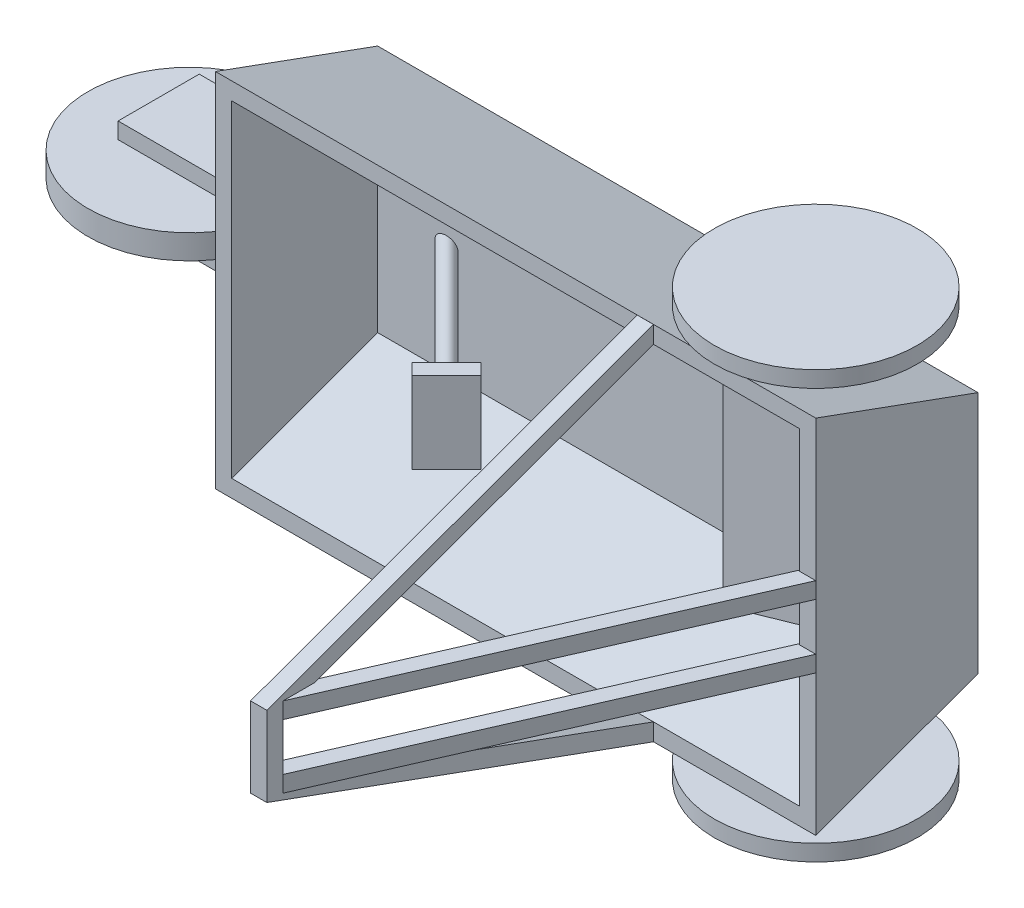
SolidWorks part; units mm, degrees
ref_plane "Front" through (0, 0, 0) normal (0, 0, 1) x (1, 0, 0)
ref_plane "Top" through (0, 0, 0) normal (0, 1, 0) x (1, 0, 0)
ref_plane "Right" through (0, 0, 0) normal (1, 0, 0) x (0, 0, -1)
sketch "Sketch1" plane through (0, 0, 0) normal (0, 0, 1) x (1, 0, 0)
  line L1 (0, 0) -> (-88.9, 0)
  line L2 (0, 0) -> (0, 38.1)
  line L3 (0, 38.1) -> (-88.9, 38.1)
  line L4 (-88.9, 0) -> (-88.9, 38.1)
  dimension "D1" = 88.9
  dimension "D2" = 38.1
extrude "Boss-Extrude1" add sketch "Sketch1" along normal blind 2.54
sketch "Sketch2" plane through (-88.9, 0, 0) normal (-1, 0, 0) x (0, 0, 1)
  line L0 (0, 0) -> (25.4, -9.2448)
  line L1 (25.4, -6.5418) -> (2.54, 1.7785)
  line L2 (2.54, 38.1) -> (2.54, 0) construction
  line L3 (25.4, -6.5418) -> (25.4, -9.2448)
  line L4 (2.54, 1.7785) -> (0, 0)
  line L5 (0, 38.1) -> (25.4, 47.3448)
  line L6 (25.4, 47.3448) -> (25.4, 44.6418)
  line L7 (25.4, 44.6418) -> (2.54, 36.3215)
  line L8 (2.54, 36.3215) -> (0, 38.1)
  line L9 (0, 38.1) -> (0, 0) construction
  dimension "D1" = 110
  dimension "D2" = 110
  dimension "D3" = 2.54
  dimension "D4" = 2.54
  dimension "D5" = 25.4
extrude "Boss-Extrude2" add sketch "Sketch2" against normal through all
sketch "Sketch3" plane through (0, 0, 0) normal (1, 0, 0) x (0, 0, -1)
  line L0 (-25.4, -9.2448) -> (0, 0)
  line L1 (0, 0) -> (0, 38.1)
  line L2 (0, 38.1) -> (-25.4, 47.3448)
  line L3 (-25.4, 47.3448) -> (-25.4, -9.2448)
extrude "Boss-Extrude3" add sketch "Sketch3" along normal blind 2.54
ref_plane "Plane1" through (0, 47.3448, 0) normal (0, 1, 0) x (-1, 0, 0)
sketch "Sketch5" plane through (0, 47.3448, 0) normal (0, 1, 0) x (-1, 0, 0)
  line L0 (-2.54, 0) -> (-2.54, 25.4) construction
  line L1 (-2.54, 0) -> (88.9, 0) construction
  circle A0 centre (10.16, 12.7) radius 2.54
  dimension "D2" = 5.08
  dimension "D1" = 12.7
  dimension "D3" = 12.7
extrude "Boss-Extrude4" add sketch "Sketch5" along normal blind 2.54 and the other way up to next
sketch "Sketch6" plane through (0, 49.8848, 0) normal (0, 1, 0) x (1, 0, 0)
  circle A0 centre (-10.16, -12.7) radius 15.875
  dimension "D1" = 31.75
extrude "Boss-Extrude5" add sketch "Sketch6" along normal blind 2.54
ref_plane "Plane2" through (0, 19.05, 0) normal (0, -1, 0) x (-1, 0, 0)
sketch "Sketch7" plane through (-88.9, 0, 0) normal (-1, 0, 0) x (0, 0, 1)
  line L0 (25.4, 47.3448) -> (25.4, 19.05)
  line L1 (25.4, 44.6418) -> (25.4, 47.3448) construction
  line L2 (25.4, 19.05) -> (0, 19.05)
  line L4 (25.4, 47.3448) -> (0, 38.1)
  line L5 (0, 38.1) -> (0, 19.05)
  line L6 (0, 38.1) -> (0, 0) construction
  line L9 (-41.91, 19.05) -> (41.91, 19.05) construction
extrude "Boss-Extrude6" add sketch "Sketch7" along normal blind 2.54
mirror "Mirror1" about plane through (0, 19.05, 0) normal (0, -1, 0) of "Boss-Extrude6", "Boss-Extrude5", "Boss-Extrude4"
sketch "Sketch8" plane through (-91.44, 0, 0) normal (-1, 0, 0) x (0, 0, 1)
  line L1 (17.78, 22.86) -> (5.08, 22.86)
  line L2 (17.78, 22.86) -> (17.78, 25.4)
  line L3 (17.78, 25.4) -> (5.08, 25.4)
  line L4 (5.08, 22.86) -> (5.08, 25.4)
  line L6 (5.08, 15.24) -> (17.78, 15.24)
  line L7 (5.08, 15.24) -> (5.08, 12.7)
  line L8 (5.08, 12.7) -> (17.78, 12.7)
  line L9 (17.78, 15.24) -> (17.78, 12.7)
  line L10 (0, 38.1) -> (0, 0) construction
  line L12 (12.7, 42.7224) -> (12.7, -4.6224) construction
  line L13 (25.4, 47.3448) -> (0, 38.1) construction
  line L14 (25.4, -9.2448) -> (0, 0) construction
  point P16 (12.7, 19.05)
  dimension "D4" = 2.54
  dimension "D1" = 12.7
  dimension "D2" = 12.7
  dimension "D3" = 5.08
  dimension "D5" = 2.54
  dimension "D6" = 3.81
  dimension "D7" = 3.81
extrude "Boss-Extrude7" add sketch "Sketch8" along normal blind 22.86
sketch "Sketch9" plane through (0, 12.7, 0) normal (0, -1, 0) x (-1, 0, 0)
  line L0 (114.3, -5.08) -> (114.3, -17.78) construction
  circle A0 centre (109.22, -11.6998) radius 2.54
  dimension "D1" = 5.08
  dimension "D2" = 5.08
extrude "Boss-Extrude8" add sketch "Sketch9" against normal up to surface (12.7 mm away) up to face at (-102.87, 25.4, 11.43)
sketch "Sketch11" plane through (0, 19.05, 0) normal (0, -1, 0) x (-1, 0, 0)
  circle A0 centre (109.22, -11.6998) radius 15.875
  circle A2 centre (109.22, -11.6998) radius 2.54 construction
  dimension "D1" = 31.75
extrude "Boss-Extrude9" add sketch "Sketch11" along normal blind 1.905 and the other way blind 1.905
ref_plane "Plane3" through (0, -2.9413, 8.0812) normal (0, 0.342, -0.9397) x (-1, 0, 0)
sketch "Sketch13" plane through (0, -2.9413, 8.0812) normal (0, 0.342, -0.9397) x (-1, 0, 0)
  line L0 (0, 50.6369) -> (88.9, 50.6369) construction
  line L1 (25.4, 50.6369) -> (22.86, 50.6369)
  line L2 (25.4, 50.6369) -> (25.4, 53.1705)
  line L3 (25.4, 53.1705) -> (22.86, 53.1705)
  line L4 (22.86, 50.6369) -> (22.86, 53.1705)
  line L5 (-2.54, 53.1769) -> (-2.54, 0) construction
  dimension "D1" = 2.5336
  dimension "D2" = 2.54
  dimension "D3" = 25.4
extrude "Boss-Extrude10" add sketch "Sketch13" against normal blind 63.5 and the other way up to next separate body
ref_plane "Plane4" through (0, 7.3982, 20.3263) normal (0, 0.342, 0.9397) x (-1, 0, 0)
sketch "Sketch16" plane through (0, 7.3982, 20.3263) normal (0, 0.342, 0.9397) x (-1, 0, 0)
  line L0 (0, 14.8346) -> (88.9, 14.8346) construction
  line L1 (25.4, 14.8346) -> (22.86, 14.8346)
  line L2 (25.4, 14.8346) -> (25.4, 17.3746)
  line L3 (25.4, 17.3746) -> (22.86, 17.3746)
  line L4 (22.86, 14.8346) -> (22.86, 17.3746)
  line L5 (-2.54, -35.8023) -> (-2.54, 17.3746) construction
  dimension "D1" = 27.94
  dimension "D2" = 2.54
  dimension "D3" = 2.54
extrude "Boss-Extrude12" add sketch "Sketch16" along normal blind 63.5 and the other way up to next
sketch "Sketch18" plane through (0, 19.05, 0) normal (0, -1, 0) x (-1, 0, 0)
  line L0 (25.4, -85.0705) -> (25.4, -85.9392) construction
  line L1 (25.4, -83.3992) -> (22.86, -83.3992)
  line L2 (25.4, -83.3992) -> (25.4, -85.9392)
  line L3 (25.4, -85.9392) -> (22.86, -85.9392)
  line L4 (22.86, -83.3992) -> (22.86, -85.9392)
  line L5 (25.4, -85.9392) -> (22.86, -85.9392) construction
  line L6 (22.86, -85.9392) -> (22.86, -85.0705) construction
  dimension "D1" = 2.54
extrude "Boss-Extrude14" add sketch "Sketch18" along normal up to surface and the other way up to surface
ref_plane "Plane5" through (11.4648, 0, 5.0209) normal (-0.916, 0, -0.4012) x (-0.4012, 0, 0.916)
sketch "Sketch19" plane through (11.4648, 0, 5.0209) normal (-0.916, 0, -0.4012) x (-0.4012, 0, 0.916)
  line L0 (22.2477, 47.3448) -> (22.2477, -9.2448) construction
  line L1 (87.8916, 12.7896) -> (22.2477, 12.7896)
  line L2 (87.8916, 12.7896) -> (87.8916, 15.3296)
  line L3 (87.8916, 15.3296) -> (22.2477, 15.3296)
  line L4 (22.2477, 12.7896) -> (22.2477, 15.3296)
  line L6 (87.8916, 25.3036) -> (22.2477, 25.3036)
  line L7 (87.8916, 25.3036) -> (87.8916, 22.7636)
  line L8 (87.8916, 22.7636) -> (22.2477, 22.7636)
  line L9 (22.2477, 25.3036) -> (22.2477, 22.7636)
  dimension "D1" = 2.54
  dimension "D2" = 2.54
extrude "Boss-Extrude15" add sketch "Sketch19" along normal blind 2.54
sketch "Sketch20" plane through (-25.4, 0, 0) normal (-1, 0, 0) x (0, 0, 1)
  line L1 (85.9392, 25.3036) -> (80.2877, 25.3036)
  line L2 (85.9392, 25.3036) -> (85.9392, 11.7464)
  line L3 (85.9392, 11.7464) -> (80.2877, 11.7464)
  line L4 (80.2877, 25.3036) -> (80.2877, 11.7464)
extrude "Cut-Extrude1" cut sketch "Sketch20" along normal blind 2.54
ref_plane "Plane6" through (-43.18, 0, -43.18) normal (0.7071, 0, 0.7071) x (0, -1, 0)
sketch "Sketch21" plane through (-43.18, 0, -43.18) normal (0.7071, 0, 0.7071) x (0, -1, 0)
  line L1 (-19.05, -48.895) -> (-19.05, 48.895) construction
  line L3 (-36.3215, -64.6578) -> (-1.7785, -64.6578) construction
  circle A0 centre (-19.05, -57.0378) radius 1.27
  dimension "D2" = 2.54
  dimension "D1" = 7.62
extrude "Boss-Extrude16" add sketch "Sketch21" along normal blind 39.116
sketch "Sketch22" plane through (0, 0, 0) normal (0, 0, -1) x (-1, 0, 0)
  line L1 (84.8073, 12.4754) -> (75.0849, 12.4754)
  line L2 (84.8073, 12.4754) -> (84.8073, 29.6888)
  line L3 (84.8073, 29.6888) -> (75.0849, 29.6888)
  line L4 (75.0849, 12.4754) -> (75.0849, 29.6888)
extrude "Cut-Extrude2" cut sketch "Sketch22" along normal blind 39.116
sketch "Sketch23" plane through (-15.5208, 0, -15.5208) normal (0.7071, 0, 0.7071) x (0.7071, 0, -0.7071)
  line L1 (-60.8478, 25.4) -> (-53.2278, 25.4)
  line L2 (-60.8478, 25.4) -> (-60.8478, 12.7)
  line L3 (-60.8478, 12.7) -> (-53.2278, 12.7)
  line L4 (-53.2278, 25.4) -> (-53.2278, 12.7)
  point P4 (-57.0378, 19.05)
  point P7 (-57.0378, 25.4)
  point P9 (-60.8478, 19.05)
  dimension "D1" = 12.7
  dimension "D2" = 7.62
extrude "Boss-Extrude17" add sketch "Sketch23" along normal blind 2.54
ref_plane "Plane7" through (0, 36.3215, 0) normal (0, 1, 0) x (-1, 0, 0)
sketch "Sketch25" plane through (0, 36.3215, 0) normal (0, 1, 0) x (-1, 0, 0)
  line L0 (0, 2.54) -> (27.4692, 9.9004)
  line L1 (27.4692, 9.9004) -> (29.4414, 2.54)
  line L2 (0, 2.54) -> (88.9, 2.54) construction
  line L3 (29.4414, 2.54) -> (0, 2.54)
  dimension "D1" = 90
  dimension "D2" = 15
  dimension "D3" = 7.62
extrude "Boss-Extrude18" add sketch "Sketch25" against normal up to next and the other way up to next
equation "\"D2@Sketch2\"=\"D1@Sketch2\""
equation "\"D4@Sketch2\"=\"D3@Sketch2\""
equation "\"D2@Sketch8\"=\"D1@Sketch8\""
equation "\"barExtrude\"=3.4"
equation "\"D2@Sketch19\"=\"D1@Sketch19\""
